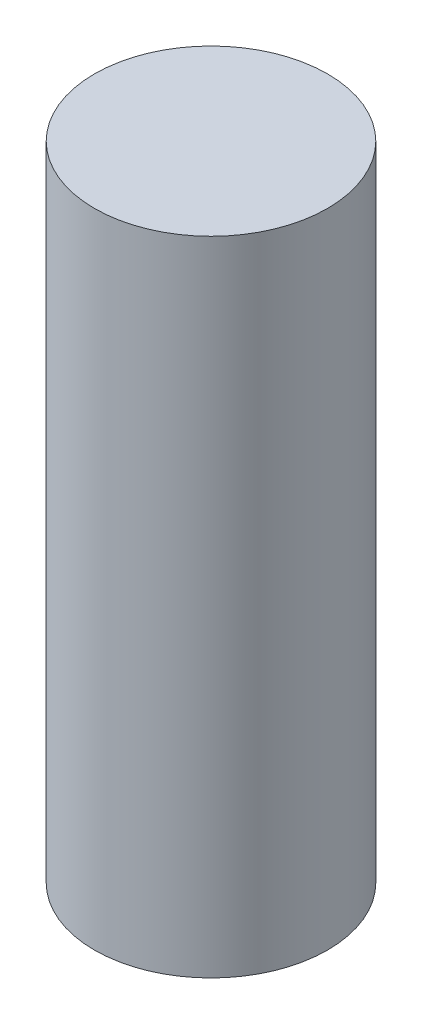
SolidWorks part; units mm, degrees
ref_plane "Front Plane" through (0, 0, 0) normal (0, 0, 1) x (1, 0, 0)
ref_plane "Top Plane" through (0, 0, 0) normal (0, 1, 0) x (1, 0, 0)
ref_plane "Right Plane" through (0, 0, 0) normal (1, 0, 0) x (0, 0, -1)
sketch "body" plane through (0, 0, 0) normal (0, 1, 0) x (1, 0, 0)
  circle A0 centre (0, 0) radius 6.35
sketch "hole" plane through (0, 0, 0) normal (0, 1, 0) x (1, 0, 0)
  circle A0 centre (0, 0) radius 3
extrude "Boss-Extrude1" add sketch "body" along normal blind 35
extrude "Cut-Extrude1" cut sketch "hole" along normal blind 10
